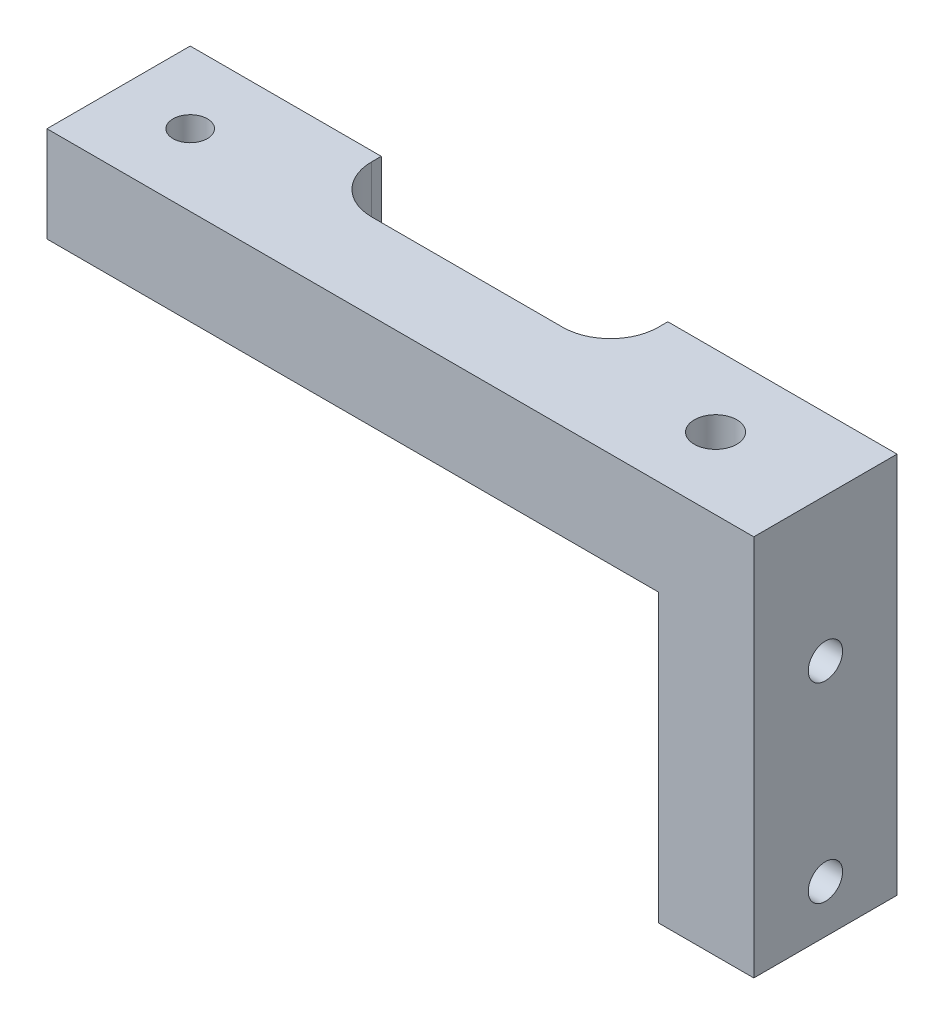
SolidWorks part; units mm, degrees
ref_plane "Front Plane" through (0, 0, 0) normal (0, 0, 1) x (1, 0, 0)
ref_plane "Top Plane" through (0, 0, 0) normal (0, 1, 0) x (1, 0, 0)
ref_plane "Right Plane" through (0, 0, 0) normal (1, 0, 0) x (0, 0, -1)
sketch "Sketch3" plane through (0, 0, 0) normal (0, 0, 1) x (1, 0, 0)
  line L1 (0, 0) -> (-44.45, 0)
  line L2 (0, 0) -> (0, 25.4)
  line L3 (0, 25.4) -> (-44.45, 25.4)
  line L4 (-44.45, 0) -> (-44.45, 25.4)
  dimension "D1" = 25.4
  dimension "D2" = 44.45
extrude "Boss-Extrude2" add sketch "Sketch3" along normal blind 9.525
sketch "Sketch4" plane through (0, 0, 9.525) normal (0, 0, 1) x (1, 0, 0)
  line L0 (0, 25.4) -> (-44.45, 25.4) construction
  line L1 (-44.45, 0) -> (-9.525, 0)
  line L2 (-44.45, 0) -> (-44.45, 15.875)
  line L3 (-44.45, 15.875) -> (-9.525, 15.875)
  line L4 (-9.525, 0) -> (-9.525, 15.875)
  line L5 (0, 0) -> (0, 25.4) construction
  dimension "D1" = 9.525
  dimension "D2" = 9.525
extrude "Cut-Extrude1" cut sketch "Sketch4" against normal through all
sketch "Sketch5" plane through (0, 0, 0) normal (1, 0, 0) x (0, 0, -1)
  line L0 (-4.7625, 0) -> (-4.7625, 25.4) construction
  line L1 (-9.525, 0) -> (0, 0) construction
  line L2 (-9.525, 25.4) -> (0, 25.4) construction
  circle A0 centre (-4.7625, 3.175) radius 1.143
  circle A1 centre (-4.7625, 15.875) radius 1.143
  dimension "D1" = 12.7
  dimension "D2" = 3.175
  dimension "D3" = 2.286
  dimension "D4" = 2.286
extrude "Cut-Extrude2" cut sketch "Sketch5" against normal blind 9.525
sketch "Sketch6" plane through (0, 15.875, 0) normal (0, -1, 0) x (1, 0, 0)
  line L1 (-44.45, 0) -> (-9.525, 0)
  line L2 (-44.45, 0) -> (-44.45, 9.525)
  line L3 (-44.45, 9.525) -> (-9.525, 9.525)
  line L4 (-9.525, 0) -> (-9.525, 9.525)
extrude "Cut-Extrude3" cut sketch "Sketch6" against normal blind 3.175
sketch "Sketch7" plane through (0, 25.4, 0) normal (0, 1, 0) x (1, 0, 0)
  line L5 (-22.225, 0) -> (-22.225, -9.525) construction
  line L7 (0, 0) -> (-44.45, 0) construction
  line L8 (0, -9.525) -> (-44.45, -9.525) construction
  line L10 (-31.75, -3.81) -> (-12.7, -3.81)
  line L11 (-31.75, -3.81) -> (-31.75, 0)
  line L12 (-31.75, 0) -> (-12.7, 0)
  line L13 (-12.7, -3.81) -> (-12.7, 0)
  line L14 (-31.75, -3.81) -> (-12.7, 0) construction
  line L15 (-31.75, 0) -> (-12.7, -3.81) construction
  point P6 (-22.225, -1.905)
  dimension "D1" = 3.81
  dimension "D2" = 19.05
extrude "Cut-Extrude4" cut sketch "Sketch7" against normal through all
fillet "Fillet1" radius 3.175 2 edges at (-12.7, 22.225, 3.81) (-31.75, 22.225, 3.81)
sketch "Sketch8" plane through (0, 25.4, 0) normal (0, 1, 0) x (1, 0, 0)
  line L0 (-22.225, -9.525) -> (-22.225, 0) construction
  line L1 (0, -9.525) -> (-44.45, -9.525) construction
  line L2 (-44.45, -4.7625) -> (0, -4.7625) construction
  line L3 (-44.45, -9.525) -> (-44.45, 0) construction
  line L4 (0, -9.525) -> (0, 0) construction
  circle A0 centre (-39.6875, -4.7625) radius 1.143
  circle A1 centre (-4.7625, -4.7625) radius 1.4135
  point P14 (0, 0)
  point P15 (-8.9104, -4.7625)
  dimension "D1" = 34.925
  dimension "D2" = 2.286
  dimension "D3" = 34.925
extrude "Cut-Extrude5" cut sketch "Sketch8" against normal blind 9.525
sketch "Sketch9" plane through (0, 0, 0) normal (1, 0, 0) x (0, 0, -1)
  line L1 (-9.525, 25.4) -> (0, 25.4)
  line L2 (-9.525, 25.4) -> (-9.525, 0)
  line L3 (-9.525, 0) -> (0, 0)
  line L4 (0, 25.4) -> (0, 0)
  circle A0 centre (-4.7625, 15.875) radius 1.143
  circle A1 centre (-4.7625, 3.175) radius 1.143
extrude "Boss-Extrude3" add sketch "Sketch9" along normal blind 2.54
sketch "Sketch10" plane through (-9.525, 0, 0) normal (-1, 0, 0) x (0, 0, 1)
  line L1 (0, 0) -> (9.525, 0)
  line L2 (0, 0) -> (0, 19.05)
  line L3 (0, 19.05) -> (9.525, 19.05)
  line L4 (9.525, 0) -> (9.525, 19.05)
  circle A0 centre (4.7625, 15.875) radius 1.143
  circle A1 centre (4.7625, 3.175) radius 1.143
extrude "Cut-Extrude6" cut sketch "Sketch10" against normal blind 5.715
